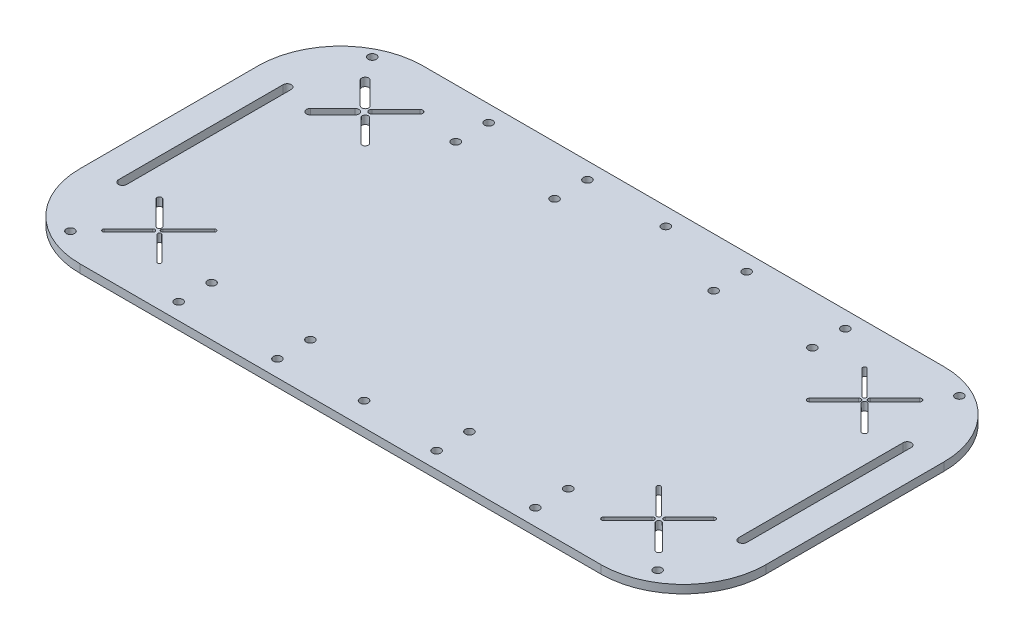
SolidWorks part; units mm, degrees
ref_plane "前视基准面" through (0, 0, 0) normal (0, 0, 1) x (1, 0, 0)
ref_plane "上视基准面" through (0, 0, 0) normal (0, 1, 0) x (1, 0, 0)
ref_plane "右视基准面" through (0, 0, 0) normal (1, 0, 0) x (0, 0, -1)
sketch "草图1" plane through (0, 0, 0) normal (0, 1, 0) x (1, 0, 0)
  line L1 (-108.3547, 61.4316) -> (81.6453, 61.4316)
  line L2 (-138.3547, 31.4316) -> (-138.3547, -33.5684)
  line L3 (-108.3547, -63.5684) -> (81.6453, -63.5684)
  line L4 (111.6453, 31.4316) -> (111.6453, -33.5684)
  arc A0 (81.6453, -63.5684) -> (111.6453, -33.5684) centre (81.6453, -33.5684) ccw
  arc A1 (81.6453, 61.4316) -> (111.6453, 31.4316) centre (81.6453, 31.4316) cw
  arc A2 (-138.3547, -33.5684) -> (-108.3547, -63.5684) centre (-108.3547, -33.5684) ccw
  arc A3 (-108.3547, 61.4316) -> (-138.3547, 31.4316) centre (-108.3547, 31.4316) ccw
  point P6 (111.6453, -63.5684)
  point P9 (111.6453, 61.4316)
  point P14 (-138.3547, 61.4316)
  dimension "D3" = 30
  dimension "D1" = 125
  dimension "D2" = 250
extrude "凸台-拉伸1" add sketch "草图1" along normal blind 3
sketch "草图2" plane through (0, 3, 0) normal (0, 1, 0) x (1, 0, 0)
  line L0 (-138.3547, 31.4316) -> (-138.3547, -33.5684) construction
  line L1 (-108.3547, -63.5684) -> (81.6453, -63.5684) construction
  line L2 (111.6453, -33.5684) -> (111.6453, 31.4316) construction
  line L3 (81.6453, 61.4316) -> (-108.3547, 61.4316) construction
  circle A0 centre (-78.3547, -45.5684) radius 1.5
  circle A1 centre (-78.3547, -57.5684) radius 1.5
  circle A2 centre (51.6453, -45.5684) radius 1.5
  circle A3 centre (51.6453, -57.5684) radius 1.5
  circle A4 centre (-78.3547, 55.4316) radius 1.5
  circle A5 centre (-78.3547, 43.4316) radius 1.5
  circle A6 centre (51.6453, 43.4316) radius 1.5
  circle A7 centre (51.6453, 55.4316) radius 1.5
  dimension "D1" = 3
  dimension "D2" = 3
  dimension "D3" = 3
  dimension "D4" = 3
  dimension "D12" = 3
  dimension "D13" = 3
  dimension "D14" = 3
  dimension "D15" = 3
  dimension "D19" = 60
  dimension "D5" = 60
  dimension "D6" = 12
  dimension "D7" = 6
  dimension "D8" = 6
  dimension "D9" = 12
  dimension "D10" = 60
  dimension "D11" = 60
  dimension "D16" = 12
  dimension "D17" = 12
  dimension "D18" = 6
  dimension "D20" = 60
extrude "切除-拉伸1" cut sketch "草图2" against normal blind 3
sketch "草图3" plane through (0, 3, 0) normal (0, 1, 0) x (1, 0, 0)
  line L0 (-126.3547, -30) -> (-126.3547, 30) construction
  line L1 (-127.8547, -30) -> (-127.8547, 30)
  line L2 (-124.8547, -30) -> (-124.8547, 30)
  line L3 (-138.3547, 31.4316) -> (-138.3547, -33.5684) construction
  line L4 (-1.65, 0) -> (1.65, 0) construction
  line L5 (99.6453, -30) -> (99.6453, 30) construction
  line L6 (98.1453, -30) -> (98.1453, 30)
  line L7 (101.1453, -30) -> (101.1453, 30)
  line L8 (111.6453, -33.5684) -> (111.6453, 31.4316) construction
  line L9 (-108.3547, -63.5684) -> (81.6453, -63.5684) construction
  line L10 (67.6453, -48.5684) -> (87.6453, -48.5684) construction
  line L11 (67.6453, -48.5684) -> (67.6453, -28.5684) construction
  line L12 (67.6453, -28.5684) -> (87.6453, -28.5684) construction
  line L13 (87.6453, -48.5684) -> (87.6453, -28.5684) construction
  line L14 (67.6453, -48.5684) -> (87.6453, -28.5684) construction
  line L15 (67.6453, -28.5684) -> (87.6453, -48.5684) construction
  line L16 (87.6453, 26.4316) -> (67.6453, 26.4316) construction
  line L17 (87.6453, 26.4316) -> (87.6453, 46.4316) construction
  line L18 (87.6453, 46.4316) -> (67.6453, 46.4316) construction
  line L19 (67.6453, 26.4316) -> (67.6453, 46.4316) construction
  line L20 (87.6453, 26.4316) -> (67.6453, 46.4316) construction
  line L21 (87.6453, 46.4316) -> (67.6453, 26.4316) construction
  line L22 (-114.3547, -48.5684) -> (-94.3547, -48.5684) construction
  line L23 (-114.3547, -48.5684) -> (-114.3547, -28.5684) construction
  line L24 (-114.3547, -28.5684) -> (-94.3547, -28.5684) construction
  line L25 (-94.3547, -48.5684) -> (-94.3547, -28.5684) construction
  line L26 (-114.3547, -48.5684) -> (-94.3547, -28.5684) construction
  line L27 (-114.3547, -28.5684) -> (-94.3547, -48.5684) construction
  line L28 (-94.3547, 26.4316) -> (-114.3547, 26.4316) construction
  line L29 (-94.3547, 26.4316) -> (-94.3547, 46.4316) construction
  line L30 (-94.3547, 46.4316) -> (-114.3547, 46.4316) construction
  line L31 (-114.3547, 26.4316) -> (-114.3547, 46.4316) construction
  line L32 (-94.3547, 26.4316) -> (-114.3547, 46.4316) construction
  line L33 (-94.3547, 46.4316) -> (-114.3547, 26.4316) construction
  line L34 (81.6453, 61.4316) -> (-108.3547, 61.4316) construction
  line L35 (-114.3547, -48.5684) -> (-105.5828, -39.7964) construction
  line L36 (-114.9003, -48.0228) -> (-106.1283, -39.2509)
  line L37 (-113.8091, -49.1139) -> (-105.0372, -40.342)
  line L38 (-105.5828, -37.3403) -> (-114.3547, -28.5684) construction
  line L39 (-106.1959, -37.9535) -> (-114.9679, -29.1815)
  line L40 (-104.9696, -36.7271) -> (-113.7415, -27.9552)
  line L41 (-103.1266, -39.7964) -> (-94.3547, -48.5684) construction
  line L42 (-102.6839, -39.3538) -> (-93.912, -48.1257)
  line L43 (-103.5693, -40.2391) -> (-94.7974, -49.0111)
  line L44 (-103.7398, -37.9535) -> (-94.3547, -28.5684) construction
  line L45 (-104.2172, -37.4761) -> (-94.8321, -28.091)
  line L46 (-103.2624, -38.4308) -> (-93.8773, -29.0457)
  line L47 (-114.3547, 26.4316) -> (-106.1959, 34.5904) construction
  line L48 (-115.3729, 27.4498) -> (-107.2141, 35.6086)
  line L49 (-113.3365, 25.4134) -> (-105.1778, 33.5722)
  line L50 (-106.1959, 38.2729) -> (-114.3547, 46.4316) construction
  line L51 (-107.1078, 37.361) -> (-115.2666, 45.5198)
  line L52 (-105.2841, 39.1847) -> (-113.4428, 47.3435)
  line L53 (-103.1541, 37.6322) -> (-94.3547, 46.4316) construction
  line L54 (-103.8835, 38.3617) -> (-95.0841, 47.1611)
  line L55 (-102.4246, 36.9028) -> (-93.6253, 45.7022)
  line L56 (-102.5135, 34.5904) -> (-94.3547, 26.4316) construction
  line L57 (-101.7171, 35.3867) -> (-93.5583, 27.228)
  line L58 (-103.3098, 33.794) -> (-95.1511, 25.6353)
  line L59 (67.6453, -48.5684) -> (76.4172, -39.7964) construction
  line L60 (67.0514, -47.9745) -> (75.8233, -39.2026)
  line L61 (68.2392, -49.1623) -> (77.0111, -40.3903)
  line L62 (76.553, -37.4761) -> (67.6453, -28.5684) construction
  line L63 (76.0264, -38.0028) -> (67.1186, -29.0951)
  line L64 (77.0797, -36.9494) -> (68.172, -28.0417)
  line L65 (78.8734, -39.7964) -> (87.6453, -48.5684) construction
  line L66 (79.5555, -39.1143) -> (88.3274, -47.8862)
  line L67 (78.1912, -40.4786) -> (86.9632, -49.2505)
  line L68 (78.8734, -37.3403) -> (87.6453, -28.5684) construction
  line L69 (78.3572, -36.8242) -> (87.1292, -28.0522)
  line L70 (79.3895, -37.8564) -> (88.1614, -29.0845)
  line L71 (67.6453, 26.4316) -> (76.553, 35.3394) construction
  line L72 (67.0414, 27.0356) -> (75.9491, 35.9433)
  line L73 (68.2492, 25.8277) -> (77.157, 34.7354)
  line L74 (76.553, 37.5239) -> (67.6453, 46.4316) construction
  line L75 (76.087, 37.0578) -> (67.1792, 45.9656)
  line L76 (77.0191, 37.9899) -> (68.1114, 46.8977)
  line L77 (78.7376, 35.3394) -> (87.6453, 26.4316) construction
  line L78 (79.3858, 35.9876) -> (88.2935, 27.0798)
  line L79 (78.0894, 34.6912) -> (86.9971, 25.7834)
  line L80 (78.7376, 37.5239) -> (87.6453, 46.4316) construction
  line L81 (78.0972, 38.1643) -> (87.0049, 47.072)
  line L82 (79.3779, 36.8835) -> (88.2857, 45.7913)
  arc A0 (-127.8547, -30) -> (-124.8547, -30) centre (-126.3547, -30) ccw
  arc A1 (-124.8547, 30) -> (-127.8547, 30) centre (-126.3547, 30) ccw
  arc A2 (98.1453, -30) -> (101.1453, -30) centre (99.6453, -30) ccw
  arc A3 (101.1453, 30) -> (98.1453, 30) centre (99.6453, 30) ccw
  arc A5 (-114.9003, -48.0228) -> (-113.8091, -49.1139) centre (-114.3547, -48.5684) ccw
  arc A6 (-105.0372, -40.342) -> (-106.1283, -39.2509) centre (-105.5828, -39.7964) ccw
  arc A7 (-106.1959, -37.9535) -> (-104.9696, -36.7271) centre (-105.5828, -37.3403) ccw
  arc A8 (-113.7415, -27.9552) -> (-114.9679, -29.1815) centre (-114.3547, -28.5684) ccw
  arc A9 (-102.6839, -39.3538) -> (-103.5693, -40.2391) centre (-103.1266, -39.7964) ccw
  arc A10 (-94.7974, -49.0111) -> (-93.912, -48.1257) centre (-94.3547, -48.5684) ccw
  arc A11 (-104.2172, -37.4761) -> (-103.2624, -38.4308) centre (-103.7398, -37.9535) ccw
  arc A12 (-93.8773, -29.0457) -> (-94.8321, -28.091) centre (-94.3547, -28.5684) ccw
  arc A13 (-115.3729, 27.4498) -> (-113.3365, 25.4134) centre (-114.3547, 26.4316) ccw
  arc A14 (-105.1778, 33.5722) -> (-107.2141, 35.6086) centre (-106.1959, 34.5904) ccw
  arc A15 (-107.1078, 37.361) -> (-105.2841, 39.1847) centre (-106.1959, 38.2729) ccw
  arc A16 (-113.4428, 47.3435) -> (-115.2666, 45.5198) centre (-114.3547, 46.4316) ccw
  arc A17 (-103.8835, 38.3617) -> (-102.4246, 36.9028) centre (-103.1541, 37.6322) ccw
  arc A18 (-93.6253, 45.7022) -> (-95.0841, 47.1611) centre (-94.3547, 46.4316) ccw
  arc A19 (-101.7171, 35.3867) -> (-103.3098, 33.794) centre (-102.5135, 34.5904) ccw
  arc A20 (-95.1511, 25.6353) -> (-93.5583, 27.228) centre (-94.3547, 26.4316) ccw
  arc A21 (67.0514, -47.9745) -> (68.2392, -49.1623) centre (67.6453, -48.5684) ccw
  arc A22 (77.0111, -40.3903) -> (75.8233, -39.2026) centre (76.4172, -39.7964) ccw
  arc A23 (76.0264, -38.0028) -> (77.0797, -36.9494) centre (76.553, -37.4761) ccw
  arc A24 (68.172, -28.0417) -> (67.1186, -29.0951) centre (67.6453, -28.5684) ccw
  arc A25 (79.5555, -39.1143) -> (78.1912, -40.4786) centre (78.8734, -39.7964) ccw
  arc A26 (86.9632, -49.2505) -> (88.3274, -47.8862) centre (87.6453, -48.5684) ccw
  arc A27 (78.3572, -36.8242) -> (79.3895, -37.8564) centre (78.8734, -37.3403) ccw
  arc A28 (88.1614, -29.0845) -> (87.1292, -28.0522) centre (87.6453, -28.5684) ccw
  arc A29 (67.0414, 27.0356) -> (68.2492, 25.8277) centre (67.6453, 26.4316) ccw
  arc A30 (77.157, 34.7354) -> (75.9491, 35.9433) centre (76.553, 35.3394) ccw
  arc A31 (76.087, 37.0578) -> (77.0191, 37.9899) centre (76.553, 37.5239) ccw
  arc A32 (68.1114, 46.8977) -> (67.1792, 45.9656) centre (67.6453, 46.4316) ccw
  arc A33 (79.3858, 35.9876) -> (78.0894, 34.6912) centre (78.7376, 35.3394) ccw
  arc A34 (86.9971, 25.7834) -> (88.2935, 27.0798) centre (87.6453, 26.4316) ccw
  arc A35 (78.0972, 38.1643) -> (79.3779, 36.8835) centre (78.7376, 37.5239) ccw
  arc A36 (88.2857, 45.7913) -> (87.0049, 47.072) centre (87.6453, 46.4316) ccw
  point P2 (-126.3547, 0)
  point P13 (99.6453, 0)
  point P20 (77.6453, -38.5684)
  point P21 (-109.9687, -44.1824)
  point P26 (77.6453, 36.4316)
  point P31 (-104.3547, -38.5684)
  point P36 (-104.3547, 36.4316)
  point P50 (-109.9687, -32.9543)
  point P56 (-98.7407, -44.1824)
  point P62 (-99.0472, -33.2609)
  point P68 (-110.2753, 30.511)
  point P74 (-110.2753, 42.3522)
  point P80 (-98.7544, 42.0319)
  point P86 (-98.4341, 30.511)
  point P92 (72.0313, -44.1824)
  point P98 (72.0992, -33.0222)
  point P104 (83.2593, -44.1824)
  point P110 (83.2593, -32.9543)
  point P116 (72.0992, 30.8855)
  point P122 (72.0992, 41.9778)
  point P128 (83.1914, 30.8855)
  point P134 (83.1914, 41.9778)
  dimension "D4" = 1.5
  dimension "D5" = 1.5
  dimension "D1" = 12
  dimension "D2" = 60
  dimension "D3" = 30
  dimension "D6" = 12
  dimension "D7" = 30
  dimension "D8" = 60
  dimension "D9" = 25
  dimension "D10" = 25
  dimension "D11" = 20
  dimension "D12" = 20
  dimension "D13" = 20
  dimension "D14" = 20
  dimension "D15" = 34
  dimension "D16" = 34
  dimension "D17" = 25
  dimension "D18" = 25
  dimension "D19" = 34
  dimension "D20" = 34
  dimension "D21" = 20
  dimension "D22" = 20
  dimension "D23" = 20
  dimension "D24" = 20
extrude "切除-拉伸2" cut sketch "草图3" against normal blind 10
sketch "草图4" plane through (0, 3, 0) normal (0, 1, 0) x (1, 0, 0)
  line L1 (93.6453, -55) -> (-120.3547, -55) construction
  line L2 (93.6453, -55) -> (93.6453, 55) construction
  line L3 (93.6453, 55) -> (-120.3547, 55) construction
  line L4 (-120.3547, -55) -> (-120.3547, 55) construction
  line L5 (-1.65, 0) -> (1.65, 0) construction
  line L6 (111.6453, -33.5684) -> (111.6453, 31.4316) construction
  circle A0 centre (93.6453, -55) radius 1.5
  circle A1 centre (93.6453, 55) radius 1.5
  circle A2 centre (-120.3547, 55) radius 1.5
  circle A3 centre (-120.3547, -55) radius 1.5
  dimension "D5" = 3
  dimension "D6" = 3
  dimension "D7" = 3
  dimension "D8" = 3
  dimension "D1" = 110
  dimension "D2" = 214
  dimension "D3" = 18
  dimension "D4" = 55
extrude "切除-拉伸3" cut sketch "草图4" against normal through all
sketch "草图5" plane through (0, 0, 0) normal (0, -1, 0) x (1, 0, 0)
  circle A0 centre (-13.3547, 55) radius 1.5
  circle A1 centre (-13.3547, -55) radius 1.5
extrude "切除-拉伸4" cut sketch "草图5" against normal blind 10
sketch "草图6" plane through (0, 3, 0) normal (0, 1, 0) x (1, 0, 0)
  line L0 (81.6453, 61.4316) -> (-108.3547, 61.4316) construction
  line L1 (-108.3547, -63.5684) -> (81.6453, -63.5684) construction
  circle A0 centre (15.6453, 55.4316) radius 1.5
  circle A1 centre (15.6453, 43.4316) radius 1.5
  circle A2 centre (51.6453, 55.4316) radius 1.5 construction
  circle A3 centre (51.6453, 43.4316) radius 1.5 construction
  circle A4 centre (15.6453, -45.5684) radius 1.5
  circle A5 centre (15.6453, -57.5684) radius 1.5
  circle A6 centre (-42.3547, -45.5684) radius 1.5
  circle A7 centre (-42.3547, -57.5684) radius 1.5
  circle A8 centre (-42.3547, 55.4316) radius 1.5
  circle A9 centre (-42.3547, 43.4316) radius 1.5
  circle A10 centre (51.6453, -45.5684) radius 1.5 construction
  circle A11 centre (51.6453, -57.5684) radius 1.5 construction
  circle A12 centre (-78.3547, 55.4316) radius 1.5 construction
  circle A13 centre (-78.3547, 43.4316) radius 1.5 construction
  circle A14 centre (-78.3547, -45.5684) radius 1.5 construction
  circle A15 centre (-78.3547, -57.5684) radius 1.5 construction
  dimension "D1" = 3
  dimension "D2" = 3
  dimension "D4" = 36
  dimension "D5" = 36
  dimension "D6" = 6
  dimension "D7" = 3
  dimension "D8" = 3
  dimension "D9" = 3
  dimension "D10" = 3
  dimension "D11" = 3
  dimension "D12" = 3
  dimension "D15" = 36
  dimension "D16" = 36
  dimension "D18" = 36
  dimension "D23" = 36
  dimension "D24" = 36
  dimension "D3" = 12
  dimension "D13" = 12
  dimension "D14" = 6
  dimension "D17" = 36
  dimension "D19" = 6
  dimension "D20" = 12
  dimension "D21" = 12
  dimension "D22" = 6
extrude "切除-拉伸5" cut sketch "草图6" against normal blind 10
